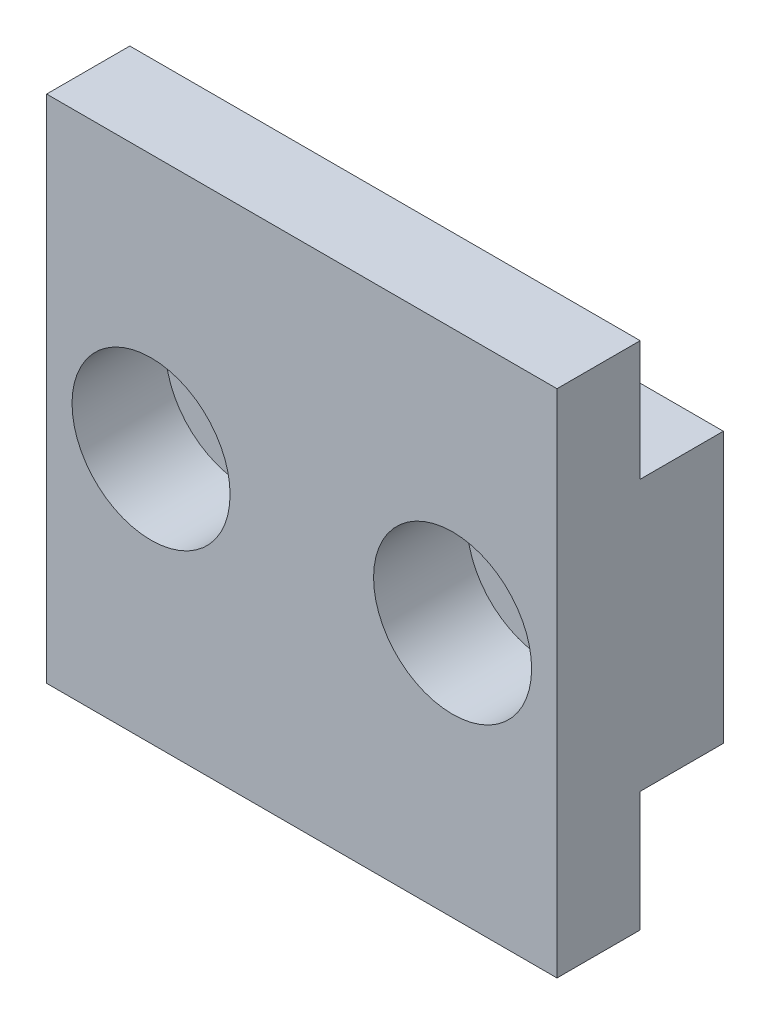
SolidWorks part; units mm, degrees
ref_plane "Front Plane" through (0, 0, 0) normal (0, 0, 1) x (1, 0, 0)
ref_plane "Top Plane" through (0, 0, 0) normal (0, 1, 0) x (1, 0, 0)
ref_plane "Right Plane" through (0, 0, 0) normal (1, 0, 0) x (0, 0, -1)
sketch "Sketch1" plane through (0, 0, 0) normal (0, 0, 1) x (1, 0, 0)
  line L0 (80, 13) -> (0.25, 13) construction
  line L1 (80, 0) -> (55.458, 0)
  line L2 (80, 0) -> (80, 13)
  line L3 (80, 13) -> (55.458, 13)
  line L4 (55.458, 0) -> (55.458, 13)
  line L5 (80, 6.5) -> (74.979, 6.5) construction
  line L6 (55.458, 6.5) -> (60.479, 6.5) construction
  point P13 (54.3848, 6.5)
extrude "Boss-Extrude1" add sketch "Sketch1" along normal blind 4
sketch "Sketch2" plane through (0, 0, 4) normal (0, 0, 1) x (1, 0, 0)
  line L0 (55.458, 13) -> (55.458, 0) construction
  line L1 (55.458, 18.771) -> (80, 18.771)
  line L2 (55.458, 18.771) -> (55.458, -5.771)
  line L3 (55.458, -5.771) -> (80, -5.771)
  line L4 (80, 18.771) -> (80, -5.771)
  line L5 (80, 0) -> (80, 13) construction
  line L6 (67.729, 18.771) -> (67.729, -5.771) construction
  line L7 (55.458, 0) -> (80, 0) construction
  point P9 (80, 6.5)
  point P12 (80, 6.5)
extrude "Boss-Extrude2" add sketch "Sketch2" along normal blind 4
sketch "Sketch3" plane through (0, 0, 0) normal (0, 0, -1) x (-1, 0, 0)
  circle A0 centre (-60.479, 6.5) radius 2.3
  circle A1 centre (-74.979, 6.5) radius 2.3
  dimension "D1" = 4.6
  dimension "D2" = 4.6
extrude "Cut-Extrude1" cut sketch "Sketch3" against normal through all
sketch "Sketch4" plane through (0, 0, 8) normal (0, 0, 1) x (1, 0, 0)
  circle A0 centre (60.479, 6.5) radius 3.8
  circle A1 centre (74.979, 6.5) radius 3.8
  dimension "D1" = 7.6
  dimension "D2" = 7.6
extrude "Cut-Extrude2" cut sketch "Sketch4" against normal blind 4.5
